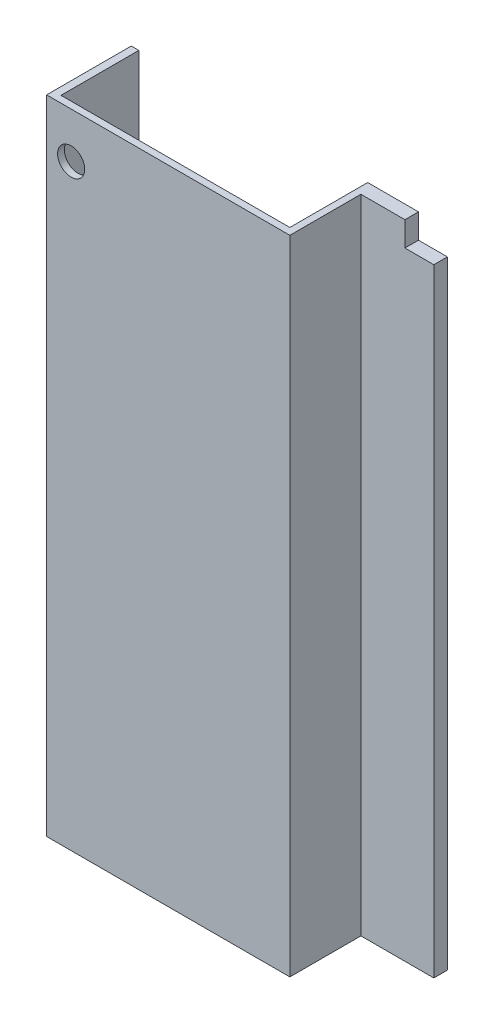
SolidWorks part; units mm, degrees
material "Polyurethane Foam Rigid"
ref_plane "Front Plane" through (0, 0, 0) normal (0, 0, 1) x (1, 0, 0)
ref_plane "Top Plane" through (0, 0, 0) normal (0, 1, 0) x (1, 0, 0)
ref_plane "Right Plane" through (0, 0, 0) normal (1, 0, 0) x (0, 0, -1)
sketch "Sketch2" plane through (0, 0, 0) normal (0, 1, 0) x (1, 0, 0)
  line L0 (-457.073, 291.592) -> (-428.625, 291.592)
  line L1 (-428.625, 291.592) -> (-428.625, 0)
  line L2 (-428.625, 0) -> (428.625, 0)
  line L3 (428.625, 0) -> (428.625, 291.592)
  line L4 (428.625, 291.592) -> (727.075, 291.592)
  line L5 (727.075, 291.592) -> (727.075, 240.792)
  line L6 (727.075, 240.792) -> (454.025, 240.792)
  line L7 (454.025, 240.792) -> (454.025, -25.4)
  line L8 (454.025, -25.4) -> (-457.073, -25.4)
  line L9 (-457.073, -25.4) -> (-457.073, 291.592)
  point P10 (0, 0)
  dimension "D1" = 50.8
  dimension "D2" = 28.448
  dimension "D3" = 1184.148
  dimension "D4" = 857.25
  dimension "D5" = 291.592
  dimension "D6" = 25.4
  dimension "D7" = 25.4
extrude "Boss-Extrude1" add sketch "Sketch2" along normal blind 2405.888
sketch "Sketch3" plane through (0, 0, -240.792) normal (0, 0, 1) x (1, 0, 0)
  line L0 (454.025, 2405.888) -> (727.075, 2405.888) construction
  line L1 (727.075, 2405.888) -> (727.075, 0) construction
  line L2 (727.075, 2405.888) -> (618.871, 2405.888)
  line L3 (727.075, 2405.888) -> (727.075, 2313.94)
  line L4 (727.075, 2313.94) -> (618.871, 2313.94)
  line L5 (618.871, 2405.888) -> (618.871, 2313.94)
  line L6 (727.075, 2405.888) -> (618.871, 2313.94) construction
  line L7 (727.075, 2313.94) -> (618.871, 2405.888) construction
  point P1 (672.973, 2359.914)
  dimension "D1" = 108.204
  dimension "D2" = 91.948
extrude "Cut-Extrude1" cut sketch "Sketch3" against normal up to surface (50.8 mm away) up to face at (577.85, 1202.944, -291.592)
sketch "Sketch4" plane through (0, 0, 25.4) normal (0, 0, 1) x (1, 0, 0)
  line L0 (-457.073, 2405.888) -> (-457.073, 0) construction
  line L1 (-457.073, 2405.888) -> (454.025, 2405.888) construction
  circle A0 centre (-365.125, 2235.708) radius 50.8
  dimension "D2" = 101.6
  dimension "D1" = 91.948
  dimension "D3" = 170.18
extrude "Cut-Extrude2" cut sketch "Sketch4" against normal up to surface (25.4 mm away) up to face at (0, 1202.944, 0)
